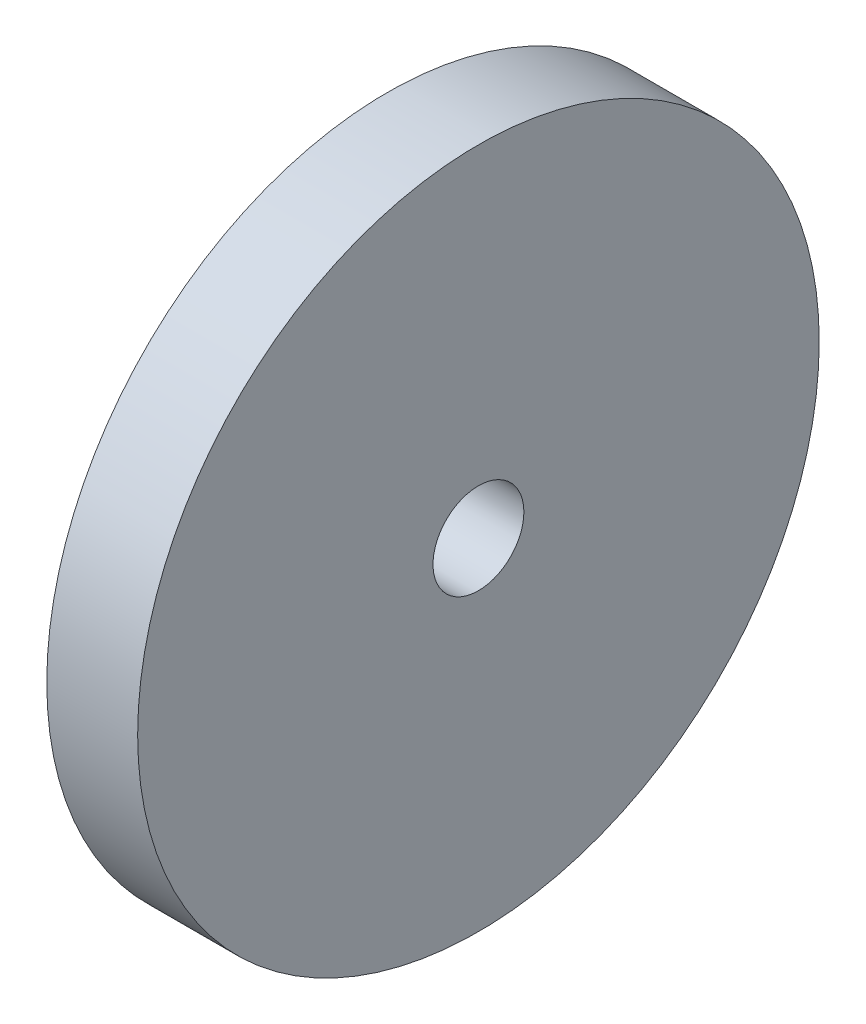
SolidWorks part; units mm, degrees
material "PMMA"
ref_plane "Front Plane" through (0, 0, 0) normal (0, 0, 1) x (1, 0, 0)
ref_plane "Top Plane" through (0, 0, 0) normal (0, 1, 0) x (1, 0, 0)
ref_plane "Right Plane" through (0, 0, 0) normal (1, 0, 0) x (0, 0, -1)
sketch "Schizzo1" plane through (0, 0, 0) normal (1, 0, 0) x (0, 0, -1)
  circle A0 centre (0, 0) radius 30
  dimension "D1" = 60
extrude "Estrusione-Estrusione1" add sketch "Schizzo1" along normal blind 8
sketch "Schizzo3" plane through (8, 0, 0) normal (1, 0, 0) x (0, 0, -1)
  circle A0 centre (0, 0) radius 4
  dimension "D1" = 8
extrude "Taglio-Estrusione1" cut sketch "Schizzo3" against normal through all
fillet "Raccordo1" [suppressed] radius 2
equation "\"Thickness8\"=8"
equation "\"D1@Estrusione-Estrusione1\"=\"Thickness8\""
